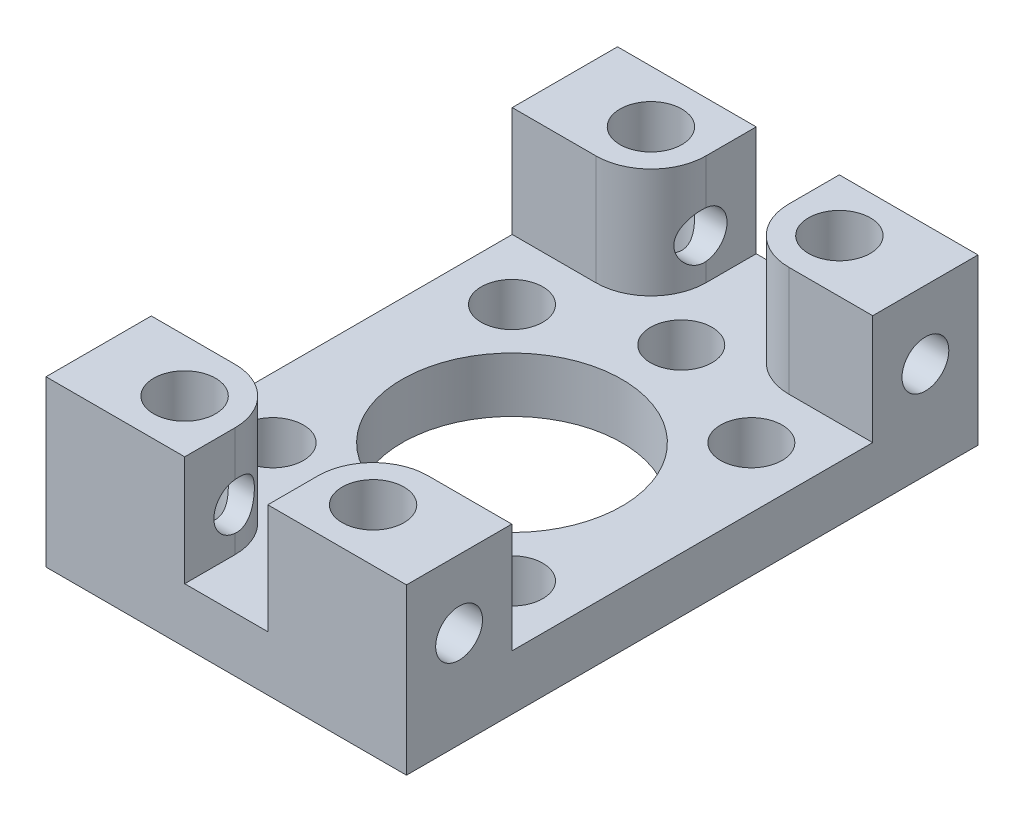
SolidWorks part; units mm, degrees
material "6061 Alloy"
ref_plane "Front Plane" through (0, 0, 0) normal (0, 0, 1) x (1, 0, 0)
ref_plane "Top Plane" through (0, 0, 0) normal (0, 1, 0) x (1, 0, 0)
ref_plane "Right Plane" through (0, 0, 0) normal (1, 0, 0) x (0, 0, -1)
sketch "Sketch1" plane through (0, 0, 0) normal (0, 1, 0) x (1, 0, 0)
  line L1 (-10.414, -16.51) -> (10.414, -16.51)
  line L2 (-10.414, -16.51) -> (-10.414, 16.51)
  line L3 (-10.414, 16.51) -> (10.414, 16.51)
  line L4 (10.414, -16.51) -> (10.414, 16.51)
  line L5 (-10.414, -16.51) -> (10.414, 16.51) construction
  line L6 (-10.414, 16.51) -> (10.414, -16.51) construction
  circle A0 centre (0, 0) radius 6.35
  circle A1 centre (0, 9.779) radius 1.778
  circle A2 centre (6.9148, 6.9148) radius 1.778
  circle A3 centre (9.779, 0) radius 1.778 [skipped]
  circle A4 centre (6.9148, -6.9148) radius 1.778
  circle A5 centre (0, -9.779) radius 1.778
  circle A6 centre (-6.9148, -6.9148) radius 1.778
  circle A7 centre (-9.779, 0) radius 1.778 [skipped]
  circle A8 centre (-6.9148, 6.9148) radius 1.778
  point P0 (0, 0)
  dimension "D3" = 9.779
  dimension "D1" = 33.02
  dimension "D2" = 20.828
  dimension "D4" = 8
extrude "Boss-Extrude1" add sketch "Sketch1" along normal blind 3.175
sketch "Sketch2" plane through (0, 3.175, 0) normal (0, 1, 0) x (1, 0, 0)
  line L0 (0, 16.51) -> (0, -16.51) construction
  line L1 (-10.414, -16.51) -> (-2.4003, -16.51)
  line L2 (-10.414, -16.51) -> (-10.414, -10.4267)
  line L3 (-10.414, -10.4267) -> (-5.5753, -10.4267)
  line L4 (-2.4003, -16.51) -> (-2.4003, -13.6017)
  line L5 (10.414, 16.51) -> (-10.414, 16.51) construction
  line L6 (-10.414, -16.51) -> (10.414, -16.51) construction
  line L7 (-10.414, 0) -> (10.414, 0) construction
  line L8 (-10.414, 16.51) -> (-10.414, -16.51) construction
  line L9 (10.414, -16.51) -> (10.414, 16.51) construction
  line L10 (2.4003, -16.51) -> (2.4003, -13.6017)
  line L11 (10.414, -10.4267) -> (5.5753, -10.4267)
  line L12 (10.414, -16.51) -> (10.414, -10.4267)
  line L13 (10.414, -16.51) -> (2.4003, -16.51)
  line L14 (10.414, 16.51) -> (2.4003, 16.51)
  line L15 (10.414, 16.51) -> (10.414, 10.4267)
  line L16 (10.414, 10.4267) -> (5.5753, 10.4267)
  line L17 (2.4003, 16.51) -> (2.4003, 13.6017)
  line L18 (-2.4003, 16.51) -> (-2.4003, 13.6017)
  line L19 (-10.414, 10.4267) -> (-5.5753, 10.4267)
  line L20 (-10.414, 16.51) -> (-10.414, 10.4267)
  line L21 (-10.414, 16.51) -> (-2.4003, 16.51)
  arc A0 (-5.5753, -10.4267) -> (-2.4003, -13.6017) centre (-5.5753, -13.6017) cw
  arc A1 (5.5753, -10.4267) -> (2.4003, -13.6017) centre (5.5753, -13.6017) ccw
  arc A2 (5.5753, 10.4267) -> (2.4003, 13.6017) centre (5.5753, 13.6017) cw
  arc A3 (-5.5753, 10.4267) -> (-2.4003, 13.6017) centre (-5.5753, 13.6017) ccw
  dimension "D2" = 3.175
  dimension "D1" = 10.4267
  dimension "D3" = 5.5753
extrude "Boss-Extrude2" add sketch "Sketch2" along normal blind 6.35
hole_wizard "9/64 (0.14063) Diameter Hole1" positions "Sketch4" profile "Sketch3" hole size "9/64" standard "Ansi Inch" end condition up to next
sketch "Sketch4" plane through (0, 9.525, 0) normal (0, 1, 0) x (-1, 0, 0)
  line L0 (18.9149, 0) -> (-18.9149, 0) construction
  line L1 (-18.9149, 0) -> (-5.4445, 13.4704) construction
  line L3 (-18.9149, 0) -> (-5.4445, -13.4704) construction
  line L4 (0, 0) -> (0, 2.5019) construction
  line L5 (18.9149, 0) -> (5.4445, -13.4704) construction
  line L6 (18.9149, 0) -> (5.4445, 13.4704) construction
  point P0 (5.4445, -13.4704)
  point P1 (-5.4445, -13.4704)
  point P4 (-5.4445, 13.4704)
  point P7 (5.4445, 13.4704)
sketch "Sketch3" plane through (-5.4445, 9.525, -13.4704) normal (1, 0, 0) x (0, 0, 1)
  line L0 (0, 0) -> (0, 9.525)
  line L1 (0, 9.525) -> (1.786, 9.525)
  line L2 (1.786, 9.525) -> (1.786, 0)
  line L5 (1.786, 0) -> (0, 0)
  line L11 (0, -6.35) -> (0, 107.95) construction
  dimension "Thru Hole Dia." = 3.572
  dimension "Thru Hole Depth" = 9.525
sketch "Sketch5" plane through (0, 0, 0) normal (1, 0, 0) x (0, 0, -1)
  line L0 (-16.51, 5.588) -> (16.51, 5.588) construction
  line L1 (-16.51, 9.525) -> (-16.51, 0) construction
  line L2 (16.51, 9.525) -> (16.51, 0) construction
  line L3 (-16.51, 0) -> (16.51, 0) construction
  line L4 (0, 0) -> (0, 19.0584) construction
  line L5 (0, 19.0584) -> (-13.4704, 5.588) construction
  line L6 (0, 19.0584) -> (13.4704, 5.588) construction
  dimension "D1" = 5.588
  dimension "D2" = 19.05
  dimension "D3" = 45
hole_wizard "#6-32 Tapped Hole1" positions "Sketch7" profile "Sketch6" tap size "#6-32" standard "Ansi Inch"
sketch "Sketch7" plane through (10.414, 0, 0) normal (1, 0, 0) x (0, 0, -1)
  point P0 (-13.4704, 5.588)
  point P1 (13.4704, 5.588)
cosmetic thread "Hole Thread1" parameters "D1"=7.0104, "D2"=3.5052
cosmetic thread "Hole Thread2" parameters "D1"=7.0104, "D2"=3.5052
sketch "Sketch6" plane through (10.414, 5.588, 13.4704) normal (0, 1, 0) x (0, 0, -1)
  line L0 (0, 0) -> (0, 8.8264)
  line L1 (0, 8.8264) -> (1.3525, 8.0137)
  line L2 (1.3525, 8.0137) -> (1.3525, 0)
  line L5 (1.3525, 0) -> (0, 0)
  line L10 (0, 8.8264) -> (-1.3526, 8.0137) construction
  line L11 (0, -6.35) -> (0, 107.95) construction
  dimension "Tap Drill Dia." = 2.7051
  dimension "Tap Drill Depth" = 8.0137
  dimension "Drill Angle" = 118
hole_wizard "#6-32 Tapped Hole2" positions "Sketch9" profile "Sketch8" tap size "#6-32" standard "Ansi Inch"
sketch "Sketch9" plane through (-10.414, 0, 0) normal (-1, 0, 0) x (0, 0, 1)
  point P0 (-13.4704, 5.588)
  point P1 (13.4704, 5.588)
cosmetic thread "Hole Thread3" parameters "D1"=3.8032, "D2"=3.5052
cosmetic thread "Hole Thread4" parameters "D1"=3.8032, "D2"=3.5052
sketch "Sketch8" plane through (-10.414, 5.588, -13.4704) normal (0, 1, 0) x (0, 0, 1)
  line L0 (0, 0) -> (0, 8.8264)
  line L1 (0, 8.8264) -> (1.3525, 8.0137)
  line L2 (1.3525, 8.0137) -> (1.3525, 0)
  line L5 (1.3525, 0) -> (0, 0)
  line L10 (0, 8.8264) -> (-1.3526, 8.0137) construction
  line L11 (0, -6.35) -> (0, 107.95) construction
  dimension "Tap Drill Dia." = 2.7051
  dimension "Tap Drill Depth" = 8.0137
  dimension "Drill Angle" = 118
